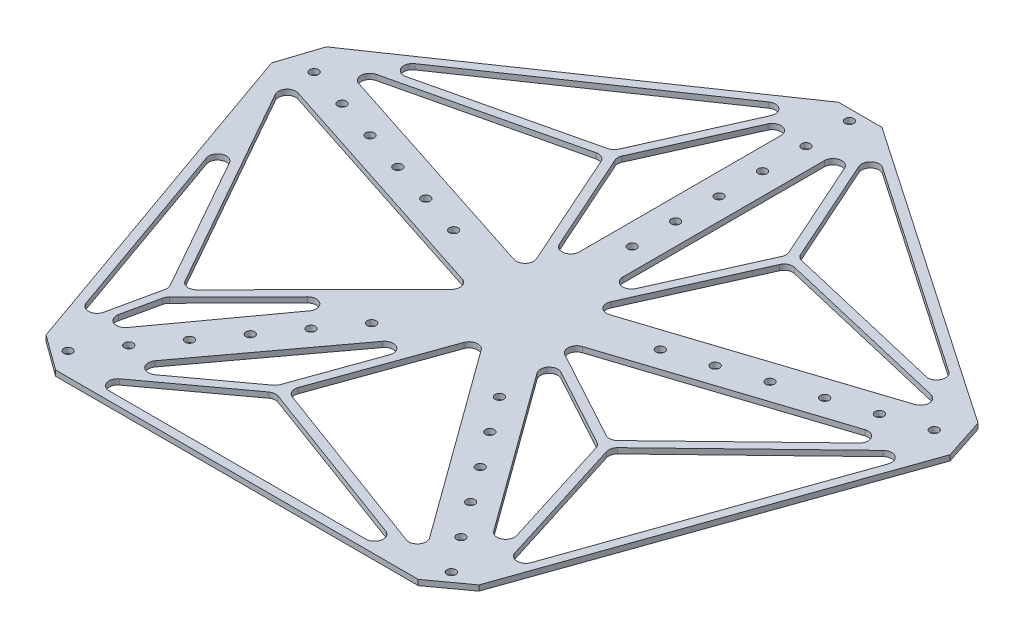
SolidWorks part; units mm, degrees
ref_plane "Front Plane" through (0, 0, 0) normal (0, 0, 1) x (1, 0, 0)
ref_plane "Top Plane" through (0, 0, 0) normal (0, 1, 0) x (1, 0, 0)
ref_plane "Right Plane" through (0, 0, 0) normal (1, 0, 0) x (0, 0, -1)
sketch "Sketch1" plane through (0, 0, 0) normal (0, 1, 0) x (1, 0, 0)
  line L0 (0, 0) -> (0, 50.8) construction
  line L1 (52.2382, 3.6196) -> (44.3892, 27.7765)
  line L2 (12.7, 50.8) -> (-12.7, 50.8)
  line L3 (12.7, 50.8) -> (12.7, 812.8)
  line L4 (12.7, 812.8) -> (-12.7, 812.8)
  line L5 (-12.7, 50.8) -> (-12.7, 812.8)
  line L6 (52.2382, 3.6196) -> (776.9433, 239.0906)
  line L7 (776.9433, 239.0906) -> (769.0942, 263.2474)
  line L8 (44.3892, 27.7765) -> (769.0942, 263.2474)
  line L9 (0, 0) -> (48.3137, 15.6981) construction
  line L10 (19.585, -48.5629) -> (40.134, -33.6332)
  line L11 (19.585, -48.5629) -> (467.4773, -665.0339)
  line L12 (467.4773, -665.0339) -> (488.0264, -650.1041)
  line L13 (40.134, -33.6332) -> (488.0264, -650.1041)
  line L14 (0, 0) -> (29.8595, -41.0981) construction
  line L15 (-40.134, -33.6332) -> (-19.585, -48.5629)
  line L16 (-40.134, -33.6332) -> (-488.0264, -650.1041)
  line L17 (-488.0264, -650.1041) -> (-467.4773, -665.0339)
  line L18 (-19.585, -48.5629) -> (-467.4773, -665.0339)
  line L19 (0, 0) -> (-29.8595, -41.0981) construction
  line L20 (-44.3892, 27.7765) -> (-52.2382, 3.6196)
  line L21 (-44.3892, 27.7765) -> (-769.0942, 263.2474)
  line L22 (-769.0942, 263.2474) -> (-776.9433, 239.0906)
  line L23 (-52.2382, 3.6196) -> (-776.9433, 239.0906)
  line L24 (0, 0) -> (-48.3137, 15.6981) construction
  circle A0 centre (0, 63.5) radius 2.54
  circle A1 centre (0, 88.9) radius 2.54
  circle A2 centre (0, 114.3) radius 2.54
  circle A3 centre (0, 139.7) radius 2.54
  circle A4 centre (0, 165.1) radius 2.54
  circle A5 centre (0, 190.5) radius 2.54
  circle A6 centre (0, 215.9) radius 2.54
  circle A7 centre (0, 241.3) radius 2.54
  circle A8 centre (0, 266.7) radius 2.54
  circle A9 centre (0, 292.1) radius 2.54
  circle A10 centre (0, 317.5) radius 2.54
  circle A11 centre (0, 342.9) radius 2.54
  circle A12 centre (0, 368.3) radius 2.54
  circle A13 centre (0, 393.7) radius 2.54
  circle A14 centre (0, 419.1) radius 2.54
  circle A15 centre (0, 444.5) radius 2.54
  circle A16 centre (0, 469.9) radius 2.54
  circle A17 centre (0, 495.3) radius 2.54
  circle A18 centre (0, 520.7) radius 2.54
  circle A19 centre (0, 546.1) radius 2.54
  circle A20 centre (0, 571.5) radius 2.54
  circle A21 centre (0, 596.9) radius 2.54
  circle A22 centre (0, 622.3) radius 2.54
  circle A23 centre (0, 647.7) radius 2.54
  circle A24 centre (0, 673.1) radius 2.54
  circle A25 centre (0, 698.5) radius 2.54
  circle A26 centre (0, 723.9) radius 2.54
  circle A27 centre (0, 749.3) radius 2.54
  circle A28 centre (0, 774.7) radius 2.54
  circle A29 centre (0, 800.1) radius 2.54
  circle A30 centre (60.3921, 19.6226) radius 2.54
  circle A31 centre (84.5489, 27.4716) radius 2.54
  circle A32 centre (108.7058, 35.3206) radius 2.54
  circle A33 centre (132.8626, 43.1697) radius 2.54
  circle A34 centre (157.0194, 51.0187) radius 2.54
  circle A35 centre (181.1763, 58.8677) radius 2.54
  circle A36 centre (205.3331, 66.7168) radius 2.54
  circle A37 centre (229.4899, 74.5658) radius 2.54
  circle A38 centre (253.6468, 82.4148) radius 2.54
  circle A39 centre (277.8036, 90.2639) radius 2.54
  circle A40 centre (301.9604, 98.1129) radius 2.54
  circle A41 centre (326.1173, 105.9619) radius 2.54
  circle A42 centre (350.2741, 113.811) radius 2.54
  circle A43 centre (374.431, 121.66) radius 2.54
  circle A44 centre (398.5878, 129.509) radius 2.54
  circle A45 centre (422.7446, 137.3581) radius 2.54
  circle A46 centre (446.9015, 145.2071) radius 2.54
  circle A47 centre (471.0583, 153.0561) radius 2.54
  circle A48 centre (495.2151, 160.9051) radius 2.54
  circle A49 centre (519.372, 168.7542) radius 2.54
  circle A50 centre (543.5288, 176.6032) radius 2.54
  circle A51 centre (567.6856, 184.4522) radius 2.54
  circle A52 centre (591.8425, 192.3013) radius 2.54
  circle A53 centre (615.9993, 200.1503) radius 2.54
  circle A54 centre (640.1561, 207.9993) radius 2.54
  circle A55 centre (664.313, 215.8484) radius 2.54
  circle A56 centre (688.4698, 223.6974) radius 2.54
  circle A57 centre (712.6266, 231.5464) radius 2.54
  circle A58 centre (736.7835, 239.3955) radius 2.54
  circle A59 centre (760.9403, 247.2445) radius 2.54
  circle A60 centre (37.3244, -51.3726) radius 2.54
  circle A61 centre (52.2541, -71.9216) radius 2.54
  circle A62 centre (67.1839, -92.4706) radius 2.54
  circle A63 centre (82.1136, -113.0197) radius 2.54
  circle A64 centre (97.0433, -133.5687) radius 2.54
  circle A65 centre (111.9731, -154.1177) radius 2.54
  circle A66 centre (126.9028, -174.6668) radius 2.54
  circle A67 centre (141.8326, -195.2158) radius 2.54
  circle A68 centre (156.7623, -215.7648) radius 2.54
  circle A69 centre (171.6921, -236.3139) radius 2.54
  circle A70 centre (186.6218, -256.8629) radius 2.54
  circle A71 centre (201.5516, -277.4119) radius 2.54
  circle A72 centre (216.4813, -297.961) radius 2.54
  circle A73 centre (231.4111, -318.51) radius 2.54
  circle A74 centre (246.3408, -339.059) radius 2.54
  circle A75 centre (261.2705, -359.6081) radius 2.54
  circle A76 centre (276.2003, -380.1571) radius 2.54
  circle A77 centre (291.13, -400.7061) radius 2.54
  circle A78 centre (306.0598, -421.2551) radius 2.54
  circle A79 centre (320.9895, -441.8042) radius 2.54
  circle A80 centre (335.9193, -462.3532) radius 2.54
  circle A81 centre (350.849, -482.9022) radius 2.54
  circle A82 centre (365.7788, -503.4513) radius 2.54
  circle A83 centre (380.7085, -524.0003) radius 2.54
  circle A84 centre (395.6383, -544.5493) radius 2.54
  circle A85 centre (410.568, -565.0984) radius 2.54
  circle A86 centre (425.4977, -585.6474) radius 2.54
  circle A87 centre (440.4275, -606.1964) radius 2.54
  circle A88 centre (455.3572, -626.7455) radius 2.54
  circle A89 centre (470.287, -647.2945) radius 2.54
  circle A90 centre (-37.3244, -51.3726) radius 2.54
  circle A91 centre (-52.2541, -71.9216) radius 2.54
  circle A92 centre (-67.1839, -92.4706) radius 2.54
  circle A93 centre (-82.1136, -113.0197) radius 2.54
  circle A94 centre (-97.0433, -133.5687) radius 2.54
  circle A95 centre (-111.9731, -154.1177) radius 2.54
  circle A96 centre (-126.9028, -174.6668) radius 2.54
  circle A97 centre (-141.8326, -195.2158) radius 2.54
  circle A98 centre (-156.7623, -215.7648) radius 2.54
  circle A99 centre (-171.6921, -236.3139) radius 2.54
  circle A100 centre (-186.6218, -256.8629) radius 2.54
  circle A101 centre (-201.5516, -277.4119) radius 2.54
  circle A102 centre (-216.4813, -297.961) radius 2.54
  circle A103 centre (-231.4111, -318.51) radius 2.54
  circle A104 centre (-246.3408, -339.059) radius 2.54
  circle A105 centre (-261.2705, -359.6081) radius 2.54
  circle A106 centre (-276.2003, -380.1571) radius 2.54
  circle A107 centre (-291.13, -400.7061) radius 2.54
  circle A108 centre (-306.0598, -421.2551) radius 2.54
  circle A109 centre (-320.9895, -441.8042) radius 2.54
  circle A110 centre (-335.9193, -462.3532) radius 2.54
  circle A111 centre (-350.849, -482.9022) radius 2.54
  circle A112 centre (-365.7788, -503.4513) radius 2.54
  circle A113 centre (-380.7085, -524.0003) radius 2.54
  circle A114 centre (-395.6383, -544.5493) radius 2.54
  circle A115 centre (-410.568, -565.0984) radius 2.54
  circle A116 centre (-425.4977, -585.6474) radius 2.54
  circle A117 centre (-440.4275, -606.1964) radius 2.54
  circle A118 centre (-455.3572, -626.7455) radius 2.54
  circle A119 centre (-470.287, -647.2945) radius 2.54
  circle A120 centre (-60.3921, 19.6226) radius 2.54
  circle A121 centre (-84.5489, 27.4716) radius 2.54
  circle A122 centre (-108.7058, 35.3206) radius 2.54
  circle A123 centre (-132.8626, 43.1697) radius 2.54
  circle A124 centre (-157.0194, 51.0187) radius 2.54
  circle A125 centre (-181.1763, 58.8677) radius 2.54
  circle A126 centre (-205.3331, 66.7168) radius 2.54
  circle A127 centre (-229.4899, 74.5658) radius 2.54
  circle A128 centre (-253.6468, 82.4148) radius 2.54
  circle A129 centre (-277.8036, 90.2639) radius 2.54
  circle A130 centre (-301.9604, 98.1129) radius 2.54
  circle A131 centre (-326.1173, 105.9619) radius 2.54
  circle A132 centre (-350.2741, 113.811) radius 2.54
  circle A133 centre (-374.431, 121.66) radius 2.54
  circle A134 centre (-398.5878, 129.509) radius 2.54
  circle A135 centre (-422.7446, 137.3581) radius 2.54
  circle A136 centre (-446.9015, 145.2071) radius 2.54
  circle A137 centre (-471.0583, 153.0561) radius 2.54
  circle A138 centre (-495.2151, 160.9051) radius 2.54
  circle A139 centre (-519.372, 168.7542) radius 2.54
  circle A140 centre (-543.5288, 176.6032) radius 2.54
  circle A141 centre (-567.6856, 184.4522) radius 2.54
  circle A142 centre (-591.8425, 192.3013) radius 2.54
  circle A143 centre (-615.9993, 200.1503) radius 2.54
  circle A144 centre (-640.1561, 207.9993) radius 2.54
  circle A145 centre (-664.313, 215.8484) radius 2.54
  circle A146 centre (-688.4698, 223.6974) radius 2.54
  circle A147 centre (-712.6266, 231.5464) radius 2.54
  circle A148 centre (-736.7835, 239.3955) radius 2.54
  circle A149 centre (-760.9403, 247.2445) radius 2.54
  point P329 (0, 0)
  dimension "D5" = 5.08
  dimension "D6" = 12.7
  dimension "D7" = 12.7
  dimension "D1" = 50.8
  dimension "D2" = 762
  dimension "D3" = 25.4
  dimension "D4" = 12.7
  dimension "D8" = 30
  dimension "D9" = 5
ref_plane "Plane1" through (0, 0, 0) normal (0, 1, 0) x (1, 0, 0)
sketch "Sketch4" plane through (0, 0, 0) normal (0, 1, 0) x (1, 0, 0)
  circle A0 centre (0, 63.5) radius 2.54
  circle A1 centre (60.3921, 19.6226) radius 2.54
  circle A2 centre (37.3244, -51.3726) radius 2.54
  circle A3 centre (-37.3244, -51.3726) radius 2.54
  circle A4 centre (-60.3921, 19.6226) radius 2.54
  circle A5 centre (0, 88.9) radius 2.54
  circle A6 centre (0, 114.3) radius 2.54
  circle A7 centre (0, 139.7) radius 2.54
  circle A8 centre (0, 165.1) radius 2.54
  circle A9 centre (0, 190.5) radius 2.54
  circle A10 centre (84.5489, 27.4716) radius 2.54
  circle A11 centre (108.7058, 35.3206) radius 2.54
  circle A12 centre (132.8626, 43.1697) radius 2.54
  circle A13 centre (157.0194, 51.0187) radius 2.54
  circle A14 centre (181.1763, 58.8677) radius 2.54
  circle A15 centre (52.2541, -71.9216) radius 2.54
  circle A16 centre (67.1839, -92.4706) radius 2.54
  circle A17 centre (82.1136, -113.0197) radius 2.54
  circle A18 centre (97.0433, -133.5687) radius 2.54
  circle A19 centre (111.9731, -154.1177) radius 2.54
  circle A20 centre (-52.2541, -71.9216) radius 2.54
  circle A21 centre (-67.1839, -92.4706) radius 2.54
  circle A22 centre (-82.1136, -113.0197) radius 2.54
  circle A23 centre (-97.0433, -133.5687) radius 2.54
  circle A24 centre (-111.9731, -154.1177) radius 2.54
  circle A25 centre (-84.5489, 27.4716) radius 2.54
  circle A26 centre (-108.7058, 35.3206) radius 2.54
  circle A27 centre (-132.8626, 43.1697) radius 2.54
  circle A28 centre (-157.0194, 51.0187) radius 2.54
  circle A29 centre (-181.1763, 58.8677) radius 2.54
  dimension "D1" = 5.08
  dimension "D2" = 5.08
  dimension "D3" = 5.08
  dimension "D4" = 5.08
  dimension "D5" = 5.08
  dimension "D7" = 25.4
  dimension "D12" = 25.4
  dimension "D13" = 25.4
  dimension "D14" = 25.4
  dimension "D15" = 25.4
  dimension "D6" = 6
  dimension "D8" = 6
  dimension "D9" = 6
  dimension "D10" = 6
  dimension "D11" = 6
sketch "Sketch5" plane through (0, 0, 0) normal (0, 1, 0) x (1, 0, 0)
  line L0 (-12.7, 196.799) -> (12.7, 196.799)
  line L1 (-12.7, 50.8) -> (-12.7, 812.8) construction
  line L2 (12.7, 50.8) -> (12.7, 812.8) construction
  line L3 (12.7, 196.799) -> (190.3987, 75.2179)
  line L4 (44.3892, 27.7765) -> (769.0942, 263.2474) construction
  line L5 (190.3987, 75.2179) -> (198.2478, 51.061)
  line L6 (52.2382, 3.6196) -> (776.9433, 239.0906) construction
  line L7 (198.2478, 51.061) -> (126.4941, -152.4977)
  line L8 (40.134, -33.6332) -> (488.0264, -650.1041) construction
  line L9 (126.4941, -152.4977) -> (105.9451, -167.4274)
  line L10 (19.585, -48.5629) -> (467.4773, -665.0339) construction
  line L11 (105.9451, -167.4274) -> (-105.9451, -167.4274)
  line L12 (-19.585, -48.5629) -> (-467.4773, -665.0339) construction
  line L13 (-105.9451, -167.4274) -> (-126.4941, -152.4977)
  line L14 (-40.134, -33.6332) -> (-488.0264, -650.1041) construction
  line L15 (-126.4941, -152.4977) -> (-198.2478, 51.061)
  line L16 (-52.2382, 3.6196) -> (-776.9433, 239.0906) construction
  line L17 (-198.2478, 51.061) -> (-190.3987, 75.2179)
  line L18 (-44.3892, 27.7765) -> (-769.0942, 263.2474) construction
  line L19 (-190.3987, 75.2179) -> (-12.7, 196.799)
  line L20 (-178.212, 77.4008) -> (-18.6456, 186.5758) construction
  line L33 (-179.8561, 71.7924) -> (-16.8082, 18.8149) construction
  line L34 (-12.7, 22.073) -> (-12.7, 187.4271) construction
  line L43 (-179.8561, 71.7924) -> (-53.7928, 101.5807) construction
  line L44 (-53.7928, 101.5807) -> (-16.8082, 18.8149) construction
  line L45 (-178.212, 77.4008) -> (-54.3848, 106.6607) construction
  line L46 (-54.3848, 106.6607) -> (-18.6456, 186.5758) construction
  line L47 (-12.7, 187.4271) -> (-49.6596, 104.783) construction
  line L48 (-49.6596, 104.783) -> (-12.7, 22.073) construction
  line L49 (0, 196.799) -> (0, 18.8142) construction
  line L50 (0, 0) -> (0, 50.8) construction
  line L51 (179.8561, 71.7924) -> (53.7928, 101.5807) construction
  line L52 (53.7928, 101.5807) -> (16.8082, 18.8149) construction
  line L53 (179.8561, 71.7924) -> (16.8082, 18.8149) construction
  line L54 (49.6596, 104.783) -> (12.7, 22.073) construction
  line L55 (12.7, 187.4271) -> (49.6596, 104.783) construction
  line L56 (12.7, 22.073) -> (12.7, 187.4271) construction
  line L57 (178.212, 77.4008) -> (54.3848, 106.6607) construction
  line L58 (54.3848, 106.6607) -> (18.6456, 186.5758) construction
  line L59 (178.212, 77.4008) -> (18.6456, 186.5758) construction
  line L68 (-110.1908, -97.7971) -> (-22.973, -10.0131) construction
  line L69 (-120.442, -144.1676) -> (-110.1908, -97.7971) construction
  line L70 (-22.973, -10.0131) -> (-120.442, -144.1676) construction
  line L71 (-188.6384, 39.0809) -> (-114.2764, -92.7443) construction
  line L72 (-114.2764, -92.7443) -> (-125.0277, -141.3771) construction
  line L73 (-188.6384, 39.0809) -> (-125.0277, -141.3771) construction
  line L74 (-187.6151, 47.6063) -> (-109.8519, -90.2484) construction
  line L75 (-109.8519, -90.2484) -> (-25.2891, -5.1367) construction
  line L76 (-187.6151, 47.6063) -> (-25.2891, -5.1367) construction
  line L77 (-100.6743, -160.1728) -> (-33.1425, -110.5568) construction
  line L78 (-3.4816, -26.3986) -> (-100.6743, -160.1728) construction
  line L79 (-33.1425, -110.5568) -> (-3.4816, -26.3986) construction
  line L80 (98.9644, -162.3474) -> (-95.0542, -162.3474) construction
  line L81 (-30.1348, -114.6507) -> (-95.0542, -162.3474) construction
  line L82 (98.9644, -162.3474) -> (-30.1348, -114.6507) construction
  line L83 (98.083, -156.6061) -> (2.4198, -24.937) construction
  line L84 (-27.6181, -110.1649) -> (2.4198, -24.937) construction
  line L85 (98.083, -156.6061) -> (-27.6181, -110.1649) construction
  line L86 (125.5526, -139.888) -> (103.7295, -43.3579) construction
  line L87 (103.7295, -43.3579) -> (192.1647, 49.0845) construction
  line L88 (125.5526, -139.888) -> (192.1647, 49.0845) construction
  line L89 (24.9165, -5.2577) -> (181.9636, 45.77) construction
  line L90 (100.3021, -39.5918) -> (24.9165, -5.2577) construction
  line L91 (181.9636, 45.77) -> (100.3021, -39.5918) construction
  line L92 (121.7049, -145.9059) -> (98.7745, -44.4781) construction
  line L93 (98.7745, -44.4781) -> (22.9095, -9.9257) construction
  line L94 (121.7049, -145.9059) -> (22.9095, -9.9257) construction
  point P61 (125.9501, -144.1668)
  point P62 (97.7845, -166.6786)
  point P63 (0, 0)
  point P64 (0, 0)
  point P67 (-298.5892, -9.0945)
  dimension "D3" = 5.08
  dimension "D4" = 5.08
  dimension "D5" = 5.08
  dimension "D6" = 5.08
  dimension "D7" = 5.08
  dimension "D8" = 5.08
  dimension "D9" = 0
  dimension "D10" = 0
  dimension "D11" = 5.08
  dimension "D12" = 5.08
  dimension "D13" = 0
  dimension "D14" = 5.08
  dimension "D15" = 0
  dimension "D16" = 5.08
  dimension "D17" = 5.842
  dimension "D18" = 5.08
  dimension "D19" = 5.08
  dimension "D20" = 5.08
  dimension "D21" = 5.1144
  dimension "D23" = 5.08
  dimension "D24" = 5.08
  dimension "D25" = 5.08
  dimension "D26" = 5.08
  dimension "D27" = 5.0845
  dimension "D28" = 5.08
  dimension "D29" = 7.5487
sketch "Sketch7" plane through (0, 0, 0) normal (0, 1, 0) x (1, 0, 0)
  line L0 (-156.047, 92.566) -> (-33.1923, 176.623)
  line L1 (-162.3176, 66.0937) -> (-27.9282, 22.428)
  line L2 (-12.7, 45.4173) -> (-12.7, 163.1488)
  line L3 (-161.916, 75.869) -> (-58.0104, 100.4214)
  line L4 (-52.2042, 97.5501) -> (-21.7204, 29.3319)
  line L5 (-152.0103, 83.4295) -> (-56.6722, 105.9576)
  line L6 (-53.203, 108.8275) -> (-25.6864, 170.3565)
  line L7 (-22.4174, 165.2227) -> (-48.7325, 106.3804)
  line L8 (-48.7331, 102.234) -> (-22.418, 43.3447)
  line L9 (162.1028, 75.9329) -> (57.9965, 100.4045)
  line L10 (52.1961, 97.5318) -> (21.7204, 29.3319)
  line L11 (162.5102, 66.1563) -> (27.9282, 22.428)
  line L12 (48.7331, 102.234) -> (22.418, 43.3447)
  line L13 (22.4174, 165.2227) -> (48.7325, 106.3804)
  line L14 (12.7, 45.4173) -> (12.7, 163.1488)
  line L15 (151.8063, 83.5717) -> (56.6896, 105.9302)
  line L16 (53.2147, 108.8015) -> (25.6864, 170.3565)
  line L17 (155.8373, 92.7095) -> (33.1923, 176.623)
  line L18 (-109.6752, -97.2781) -> (-69.4278, -56.7695)
  line L19 (-115.6312, -120.9945) -> (-111.0363, -99.7831)
  line L20 (-61.7143, -63.3359) -> (-106.5566, -125.056)
  line L21 (-160.0129, -11.7975) -> (-115.3027, -91.1378)
  line L22 (-114.7636, -94.7073) -> (-121.1364, -124.1264)
  line L23 (-169.2296, -15.9802) -> (-130.8923, -124.7397)
  line L24 (-181.2695, 36.2711) -> (-113.2257, -84.4761)
  line L25 (-105.1963, -85.5626) -> (-31.1107, -10.9961)
  line L26 (-175.2741, 43.5964) -> (-33.1446, -2.5842)
  line L27 (-74.4538, -140.756) -> (-34.7119, -111.5574)
  line L28 (-24.9138, -57.3227) -> (-81.5411, -133.635)
  line L29 (-32.9376, -109.1775) -> (-16.0521, -62.0638)
  line L30 (70.3487, -162.3474) -> (-79.7675, -162.3474)
  line L31 (-32.5458, -116.2696) -> (-82.7753, -153.1736)
  line L32 (72.1092, -152.5022) -> (-27.7774, -115.5983)
  line L33 (88.3073, -143.1512) -> (8.2236, -32.9253)
  line L34 (-26.1897, -105.4065) -> (-0.6684, -34.1973)
  line L35 (82.437, -150.9023) -> (-23.1681, -111.8856)
  line L36 (120.8118, -125.8295) -> (96.2624, -47.6655)
  line L37 (97.5819, -42.4873) -> (176.533, 33.6816)
  line L38 (130.4494, -125.9961) -> (184.8512, 28.3368)
  line L39 (36.0319, -1.6461) -> (160.6862, 38.8565)
  line L40 (88.0512, -39.6868) -> (35.1753, -10.9405)
  line L41 (165.7831, 30.3692) -> (94.0047, -38.8797)
  line L42 (112.5455, -116.4635) -> (91.3157, -48.8689)
  line L43 (88.8955, -45.9281) -> (42.8128, -20.8749)
  line L44 (103.5891, -120.9716) -> (36.2766, -28.3239)
  line L45 (-40.134, -33.6332) -> (-488.0264, -650.1041) construction
  line L46 (-52.2382, 3.6196) -> (-776.9433, 239.0906) construction
  line L47 (-44.3892, 27.7765) -> (-769.0942, 263.2474) construction
  line L48 (-12.7, 50.8) -> (-12.7, 812.8) construction
  line L49 (12.7, 50.8) -> (12.7, 812.8) construction
  line L50 (44.3892, 27.7765) -> (769.0942, 263.2474) construction
  line L51 (52.2382, 3.6196) -> (776.9433, 239.0906) construction
  line L52 (40.134, -33.6332) -> (488.0264, -650.1041) construction
  line L53 (19.585, -48.5629) -> (467.4773, -665.0339) construction
  line L54 (-126.4941, -152.4977) -> (-198.2478, 51.061) construction
  line L55 (-110.1908, -97.7971) -> (-22.973, -10.0131) construction
  line L56 (105.9451, -167.4274) -> (-105.9451, -167.4274) construction
  line L57 (198.2478, 51.061) -> (126.4941, -152.4977) construction
  line L58 (12.7, 196.799) -> (190.3987, 75.2179) construction
  line L59 (-190.3987, 75.2179) -> (-12.7, 196.799) construction
  arc A0 (88.3073, -143.1512) -> (82.437, -150.9023) centre (84.1975, -146.1371) cw
  arc A1 (70.3487, -162.3474) -> (72.1092, -152.5022) centre (70.3487, -157.2674) ccw
  arc A2 (-79.7675, -162.3474) -> (-82.7753, -153.1736) centre (-79.7675, -157.2674) cw
  arc A3 (-74.4538, -140.756) -> (-81.5411, -133.635) centre (-77.4616, -136.6622) cw
  arc A4 (-24.9138, -57.3227) -> (-16.0521, -62.0638) centre (-20.8343, -60.3499) cw
  arc A5 (8.2236, -32.9253) -> (-0.6684, -34.1973) centre (4.1138, -35.9112) ccw
  arc A6 (160.6862, 38.8565) -> (165.7831, 30.3692) centre (162.256, 34.0252) cw
  arc A7 (176.533, 33.6816) -> (184.8512, 28.3368) centre (180.0601, 30.0256) cw
  arc A8 (120.8118, -125.8295) -> (130.4494, -125.9961) centre (125.6584, -124.3073) ccw
  arc A9 (112.5455, -116.4635) -> (103.5891, -120.9716) centre (107.6989, -117.9857) cw
  arc A10 (42.8128, -20.8749) -> (36.2766, -28.3239) centre (40.3864, -25.338) ccw
  arc A11 (36.0319, -1.6461) -> (35.1753, -10.9405) centre (37.6017, -6.4775) ccw
  arc A12 (151.8063, 83.5717) -> (155.8373, 92.7095) centre (152.9687, 88.5169) ccw
  arc A13 (162.1028, 75.9329) -> (162.5102, 66.1563) centre (160.9404, 70.9877) cw
  arc A14 (21.7204, 29.3319) -> (27.9282, 22.428) centre (26.3584, 27.2593) ccw
  arc A15 (-31.1107, -10.9961) -> (-33.1446, -2.5842) centre (-34.7144, -7.4156) ccw
  arc A16 (-69.4278, -56.7695) -> (-61.7143, -63.3359) centre (-65.8241, -60.3499) cw
  arc A17 (-115.6312, -120.9945) -> (-106.5566, -125.056) centre (-110.6664, -122.07) ccw
  arc A18 (-121.1364, -124.1264) -> (-130.8923, -124.7397) centre (-126.1013, -123.0509) cw
  arc A19 (-160.0129, -11.7975) -> (-169.2296, -15.9802) centre (-164.4385, -14.2914) ccw
  arc A20 (-181.2695, 36.2711) -> (-175.2741, 43.5964) centre (-176.8439, 38.7651) cw
  arc A21 (-115.3027, -91.1378) -> (-114.7636, -94.7073) centre (-119.7284, -93.6318) cw
  arc A22 (-109.6752, -97.2781) -> (-111.0363, -99.7831) centre (-106.0715, -100.8586) ccw
  arc A23 (-113.2257, -84.4761) -> (-105.1963, -85.5626) centre (-108.8, -81.9822) ccw
  arc A24 (-34.7119, -111.5574) -> (-32.9376, -109.1775) centre (-37.7197, -107.4636) ccw
  arc A25 (-32.5458, -116.2696) -> (-27.7774, -115.5983) centre (-29.538, -120.3635) cw
  arc A26 (-26.1897, -105.4065) -> (-23.1681, -111.8856) centre (-21.4075, -107.1205) ccw
  arc A27 (96.2624, -47.6655) -> (97.5819, -42.4873) centre (101.109, -46.1433) cw
  arc A28 (91.3157, -48.8689) -> (88.8955, -45.9281) centre (86.4691, -50.3911) ccw
  arc A29 (88.0512, -39.6868) -> (94.0047, -38.8797) centre (90.4776, -35.2238) ccw
  arc A30 (57.9965, 100.4045) -> (52.1961, 97.5318) centre (56.834, 95.4593) ccw
  arc A31 (56.6896, 105.9302) -> (53.2147, 108.8015) centre (57.852, 110.8754) cw
  arc A32 (25.6864, 170.3565) -> (33.1923, 176.623) centre (30.3237, 172.4304) cw
  arc A33 (22.4174, 165.2227) -> (12.7, 163.1488) centre (17.78, 163.1488) ccw
  arc A34 (48.7331, 102.234) -> (48.7325, 106.3804) centre (44.0951, 104.3065) ccw
  arc A35 (22.418, 43.3447) -> (12.7, 45.4173) centre (17.78, 45.4173) cw
  arc A36 (-12.7, 45.4173) -> (-22.418, 43.3447) centre (-17.78, 45.4173) cw
  arc A37 (-27.9282, 22.428) -> (-21.7204, 29.3319) centre (-26.3584, 27.2593) ccw
  arc A38 (-162.3176, 66.0937) -> (-161.916, 75.869) centre (-160.7478, 70.9251) cw
  arc A39 (-156.047, 92.566) -> (-152.0103, 83.4295) centre (-153.1785, 88.3734) ccw
  arc A40 (-58.0104, 100.4214) -> (-52.2042, 97.5501) centre (-56.8422, 95.4776) cw
  arc A41 (-48.7325, 106.3804) -> (-48.7331, 102.234) centre (-44.0951, 104.3065) ccw
  arc A42 (-56.6722, 105.9576) -> (-53.203, 108.8275) centre (-57.8404, 110.9014) ccw
  arc A43 (-33.1923, 176.623) -> (-25.6864, 170.3565) centre (-30.3237, 172.4304) cw
  arc A44 (-12.7, 163.1488) -> (-22.4174, 165.2227) centre (-17.78, 163.1488) ccw
  point P119 (-114.3548, -92.8201)
  point P124 (-109.9291, -90.3261)
  point P167 (-66.5819, -59.744)
  point P168 (0, 0)
  dimension "D23" = 5.08
  dimension "D1" = 5.08
  dimension "D2" = 5.08
  dimension "D3" = 5.08
  dimension "D4" = 5.08
  dimension "D5" = 5.08
  dimension "D6" = 5.08
  dimension "D7" = 5.08
  dimension "D8" = 5.08
  dimension "D9" = 5.08
  dimension "D10" = 5.08
  dimension "D11" = 5.08
  dimension "D12" = 5.08
  dimension "D13" = 5.08
  dimension "D14" = 5.08
  dimension "D15" = 5.08
  dimension "D16" = 5.08
  dimension "D17" = 5.08
  dimension "D18" = 5.08
  dimension "D19" = 5.08
  dimension "D20" = 5.08
  dimension "D21" = 5.08
  dimension "D22" = 4.7174
extrude "Boss-Extrude2" add sketch "Sketch5" along normal blind 3.175
extrude "Cut-Extrude6" cut sketch "Sketch4" against normal through all from surface at 3.175 starting at face at (0, 3.175, -0.6306)
extrude "Cut-Extrude13" cut sketch "Sketch7" against normal through all from surface at 3.175 starting at face at (0, 3.175, -187.96)
